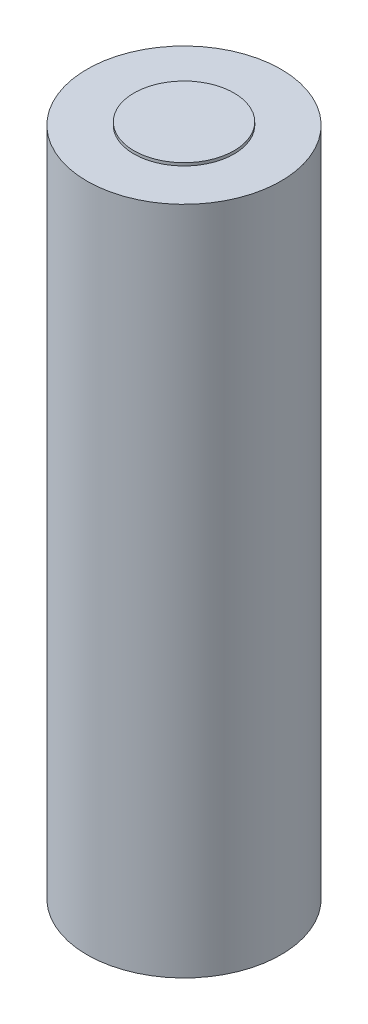
SolidWorks part; units mm, degrees
ref_plane "Front Plane" through (0, 0, 0) normal (0, 0, 1) x (1, 0, 0)
ref_plane "Top Plane" through (0, 0, 0) normal (0, 1, 0) x (1, 0, 0)
ref_plane "Right Plane" through (0, 0, 0) normal (1, 0, 0) x (0, 0, -1)
sketch "Sketch1" plane through (0, 0, 0) normal (0, 1, 0) x (1, 0, 0)
  circle A0 centre (0, 0) radius 10.175
  dimension "D1" = 20.35
extrude "Boss-Extrude1" add sketch "Sketch1" along normal blind 70.3
sketch "Sketch2" plane through (0, 70.3, 0) normal (0, 1, 0) x (1, 0, 0)
  circle A0 centre (0, 0) radius 5.25
  dimension "D1" = 10.5
extrude "Boss-Extrude2" add sketch "Sketch2" along normal blind 0.3
